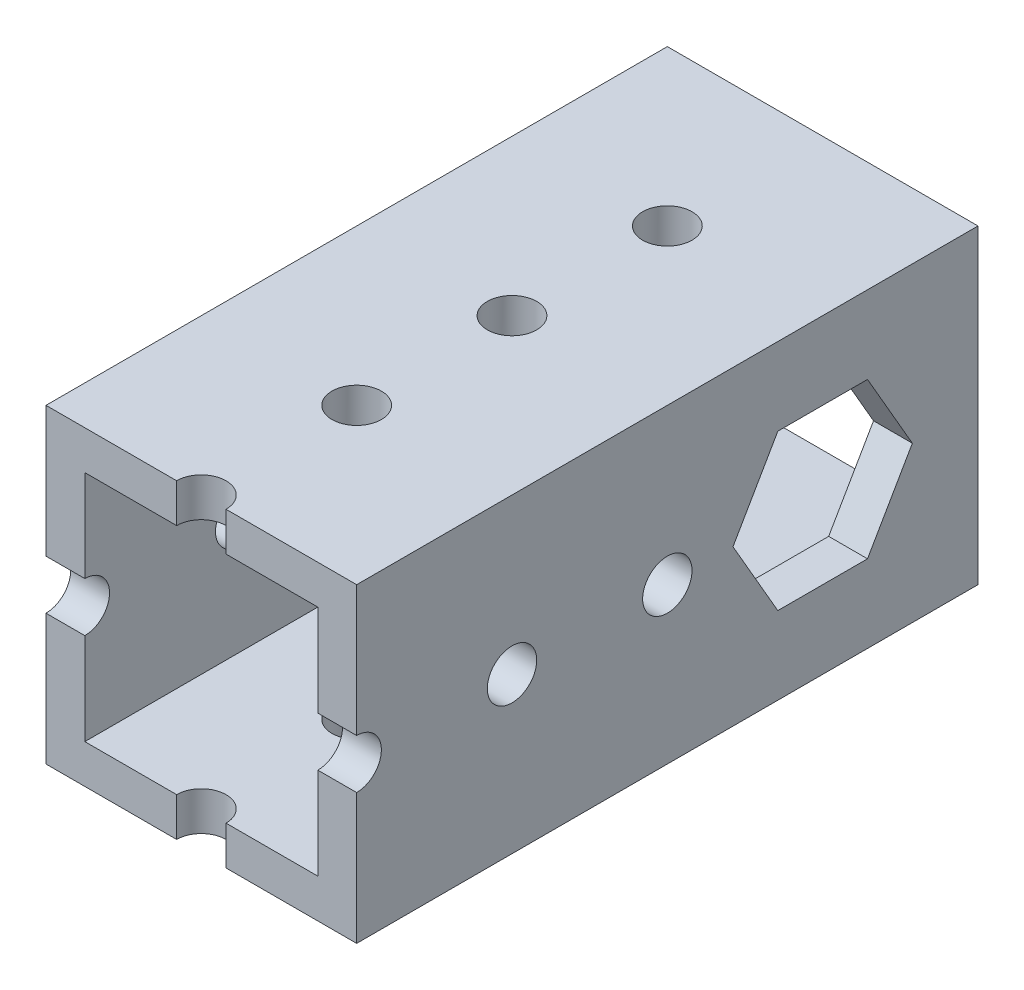
SolidWorks part; units mm, degrees
material "6061 Alloy"
ref_plane "Front Plane" through (0, 0, 0) normal (0, 0, 1) x (1, 0, 0)
ref_plane "Top Plane" through (0, 0, 0) normal (0, 1, 0) x (1, 0, 0)
ref_plane "Right Plane" through (0, 0, 0) normal (1, 0, 0) x (0, 0, -1)
sketch "Sketch1" plane through (0, 0, 0) normal (0, 0, 1) x (1, 0, 0)
  line L0 (3.175, 22.225) -> (22.225, 22.225)
  line L1 (0, 0) -> (25.4, 0)
  line L2 (0, 0) -> (0, 25.4)
  line L3 (0, 25.4) -> (25.4, 25.4)
  line L4 (25.4, 0) -> (25.4, 25.4)
  line L5 (22.225, 3.175) -> (22.225, 22.225)
  line L6 (3.175, 3.175) -> (22.225, 3.175)
  line L7 (3.175, 3.175) -> (3.175, 22.225)
  dimension "D1" = 25.4
  dimension "D2" = 25.4
  dimension "D3" = 3.175
extrude "Boss-Extrude1" add sketch "Sketch1" along normal blind 63.5
sketch "Sketch2" plane through (0, 25.4, 0) normal (0, 1, 0) x (1, 0, 0)
  line L0 (12.7, -63.5) -> (12.7, 0) construction
  line L1 (25.4, -63.5) -> (0, -63.5) construction
  line L2 (25.4, 0) -> (0, 0) construction
  circle A0 centre (12.7, -50.8) radius 2.0193
  circle A1 centre (12.7, -38.1) radius 2.0193
  circle A2 centre (12.7, -25.4) radius 2.0193
  circle A3 centre (12.7, -12.7) radius 2.0193
  dimension "D1" = 4.0386
  dimension "D2" = 12.7
  dimension "D3" = 4
extrude "Cut-Extrude1" cut sketch "Sketch2" against normal blind 63.5
sketch "Sketch3" plane through (25.4, 0, 0) normal (1, 0, 0) x (0, 0, -1)
  line L0 (-63.5, 12.7) -> (0, 12.7) construction
  line L1 (-63.5, 0) -> (-63.5, 25.4) construction
  line L2 (0, 0) -> (0, 25.4) construction
  circle A0 centre (-50.8, 12.7) radius 2.0193
  circle A1 centre (-38.1, 12.7) radius 2.0193
  circle A2 centre (-25.4, 12.7) radius 2.0193
  circle A3 centre (-12.7, 12.7) radius 2.0193
  dimension "D1" = 4.0386
  dimension "D2" = 12.7
  dimension "D3" = 4
extrude "Cut-Extrude2" cut sketch "Sketch3" against normal blind 63.5
sketch "Sketch4" plane through (25.4, 0, 0) normal (1, 0, 0) x (0, 0, -1)
  line L1 (-9.0338, 19.05) -> (-16.3662, 19.05)
  line L2 (-16.3662, 19.05) -> (-20.0323, 12.7)
  line L3 (-20.0323, 12.7) -> (-16.3662, 6.35)
  line L4 (-16.3662, 6.35) -> (-9.0338, 6.35)
  line L5 (-9.0338, 6.35) -> (-5.3677, 12.7)
  line L6 (-5.3677, 12.7) -> (-9.0338, 19.05)
  circle A0 centre (-12.7, 12.7) radius 6.35 construction
  point P1 (0, 0)
  point P10 (-8.9751, 19.05)
  dimension "D1" = 12.7
extrude "Cut-Extrude3" cut sketch "Sketch4" against normal blind 28.702
sketch "Sketch5" plane through (0, 0, 63.5) normal (0, 0, 1) x (1, 0, 0)
  line L1 (0, 25.4) -> (25.4, 25.4)
  line L2 (0, 25.4) -> (0, 0)
  line L3 (0, 0) -> (25.4, 0)
  line L4 (25.4, 25.4) -> (25.4, 0)
extrude "Cut-Extrude4" cut sketch "Sketch5" against normal blind 12.7
